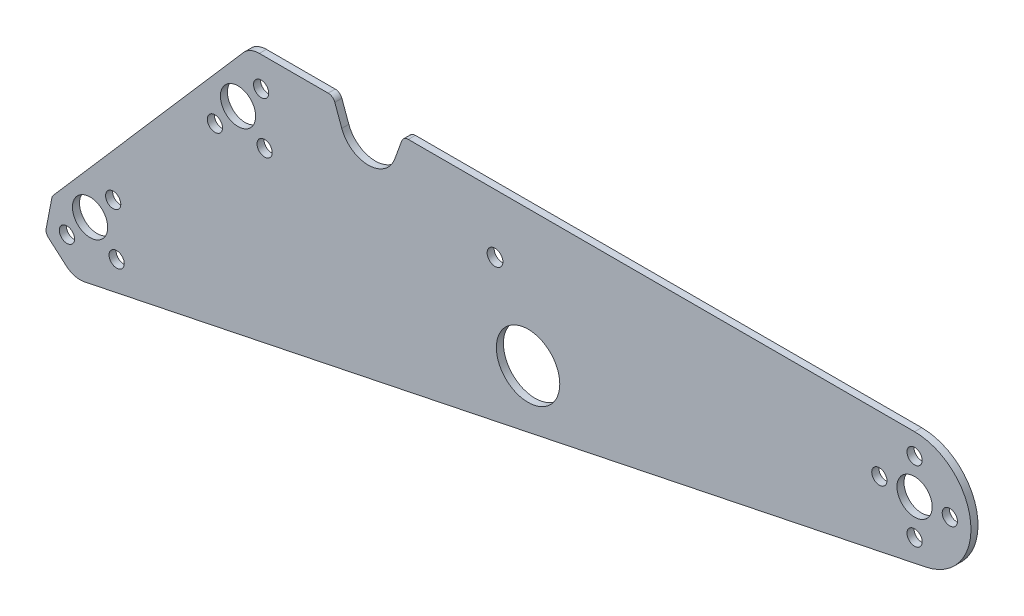
SolidWorks part; units mm, degrees
material "6061-T6 (SS)"
ref_plane "Front Plane" through (0, 0, 0) normal (0, 0, 1) x (1, 0, 0)
ref_plane "Top Plane" through (0, 0, 0) normal (0, 1, 0) x (1, 0, 0)
ref_plane "Right Plane" through (0, 0, 0) normal (1, 0, 0) x (0, 0, -1)
sketch "Sketch1" plane through (0, 0, 0) normal (0, 0, 1) x (1, 0, 0)
  line L0 (0, 0) -> (-66.6556, -76.6785) construction
  line L1 (55, 0) -> (-55, 0) construction
  line L2 (304.8, 25.4) -> (76.7244, 25.4)
  line L3 (-83.1578, -76.304) -> (2.4044, 22.124)
  line L4 (-69.2153, -103.1424) -> (309.935, -24.8755)
  line L5 (0, 15.875) -> (0, -15.875) construction
  line L6 (-15.875, 0) -> (15.875, 0) construction
  line L7 (-66.6556, -76.6785) -> (-56.2407, -64.6975) construction
  line L8 (-66.6556, -76.6785) -> (-54.6746, -87.0934) construction
  line L9 (-85.4182, -94.0237) -> (-77.3898, -101.0027)
  line L10 (304.8, 0) -> (304.8, 15.875) construction
  line L11 (0, 0) -> (-10.4149, -11.981) construction
  line L12 (0, 0) -> (11.981, -10.4149) construction
  line L13 (70.609, 14.7063) -> (73.7408, 23.3109)
  line L14 (46.7408, 14.7063) -> (43.609, 23.3109)
  line L15 (40.6255, 25.4) -> (9.593, 25.4)
  line L16 (-83.8782, -77.7812) -> (-86.4519, -91.0217)
  circle A0 centre (304.8, 0) radius 7.9375
  circle A1 centre (0, 0) radius 7.9375
  circle A2 centre (-66.6556, -76.6785) radius 7.9375
  arc A7 (304.8, 25.4) -> (309.935, -24.8755) centre (304.8, 0) cw
  arc A8 (-69.2153, -103.1424) -> (-77.3898, -101.0027) centre (-71.1409, -93.8141) cw
  arc A18 (9.593, 25.4) -> (2.4044, 22.124) centre (9.593, 15.875) ccw
  circle A19 centre (304.8, 0) radius 15.875 construction
  circle A20 centre (304.8, 15.875) radius 3.429
  circle A21 centre (320.675, 0) radius 3.429
  circle A22 centre (304.8, -15.875) radius 3.429
  circle A23 centre (288.925, 0) radius 3.429
  circle A24 centre (-66.6556, -76.6785) radius 15.875 construction
  circle A25 centre (-56.2407, -64.6975) radius 3.429
  circle A26 centre (-54.6746, -87.0934) radius 3.429
  circle A27 centre (-77.0705, -88.6595) radius 3.429
  circle A28 centre (0, 0) radius 15.875 construction
  circle A29 centre (-10.4149, -11.981) radius 3.429
  circle A30 centre (11.981, -10.4149) radius 3.429
  circle A31 centre (10.4149, 11.981) radius 3.429
  circle A32 centre (130.6713, -35.9449) radius 14.2875
  arc A33 (46.7408, 14.7063) -> (70.609, 14.7063) centre (58.6749, 19.05) ccw
  arc A34 (43.609, 23.3109) -> (40.6255, 25.4) centre (40.6255, 22.225) ccw
  arc A35 (73.7408, 23.3109) -> (76.7244, 25.4) centre (76.7244, 22.225) cw
  circle A36 centre (115.7866, -1.0874) radius 3.556
  arc A37 (-86.4519, -91.0217) -> (-85.4182, -94.0237) centre (-83.3352, -91.6275) ccw
  arc A38 (-83.8782, -77.7812) -> (-83.1578, -76.304) centre (-80.7616, -78.387) cw
  point P19 (-86.8017, -92.8211)
  point P21 (0, 0)
  point P26 (0, 0)
  point P64 (42.8487, 25.4)
  point P73 (-83.7159, -76.9461)
  dimension "D2" = 15.875
  dimension "D5" = 101.6
  dimension "D6" = 25.4
  dimension "D8" = 6.858
  dimension "D15" = 9.525
  dimension "D16" = 31.75
  dimension "D17" = 4
  dimension "D10" = 31.75
  dimension "D11" = 3
  dimension "D20" = 31.75
  dimension "D21" = 3
  dimension "D24" = 25.4
  dimension "D26" = 28.575
  dimension "D27" = 48.26
  dimension "D31" = 25.4
  dimension "D32" = 3.175
  dimension "D33" = 7.112
  dimension "D35" = 37.9025
  dimension "D38" = 3.175
  dimension "D3" = 304.8
  dimension "D4" = 131
  dimension "D7" = 31.75
  dimension "D9" = 31.75
  dimension "D12" = 25.4
  dimension "D13" = 12.7
  dimension "D14" = 25.4
  dimension "D18" = 90
  dimension "D19" = 15.875
  dimension "D22" = 90
  dimension "D23" = 15.875
  dimension "D25" = 177.8
  dimension "D28" = 6.35
  dimension "D29" = 110
  dimension "D30" = 110
  dimension "D34" = 26.4874
  dimension "D36" = 150
  dimension "D37" = 15.875
extrude "Boss-Extrude1" add sketch "Sketch1" along normal blind 3.175
